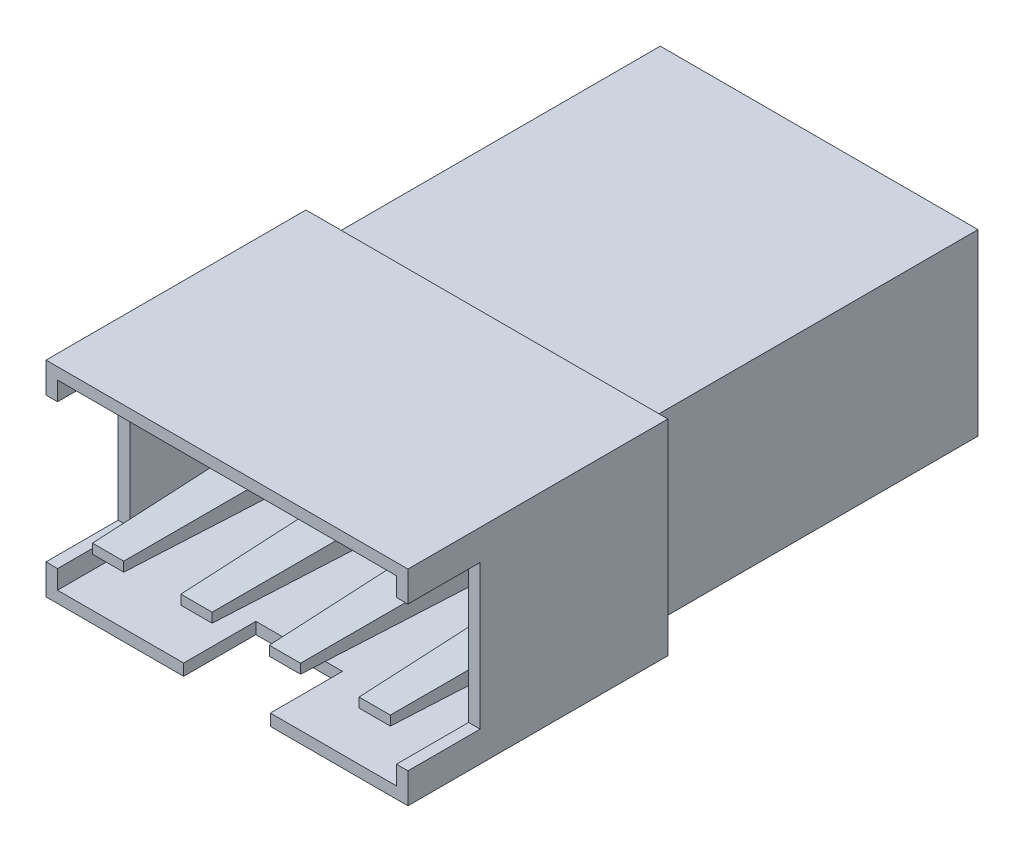
SolidWorks part; units mm, degrees
ref_plane "Front Plane" through (0, 0, 0) normal (0, 0, 1) x (1, 0, 0)
ref_plane "Top Plane" through (0, 0, 0) normal (0, 1, 0) x (1, 0, 0)
ref_plane "Right Plane" through (0, 0, 0) normal (1, 0, 0) x (0, 0, -1)
sketch "Sketch1" plane through (0, 0, 0) normal (0, 0, 1) x (1, 0, 0)
  line L1 (0, 0) -> (12.53, 0)
  line L2 (0, 0) -> (0, -7.1)
  line L3 (0, -7.1) -> (12.53, -7.1)
  line L4 (12.53, 0) -> (12.53, -7.1)
  dimension "D1" = 7.1
  dimension "D2" = 12.53
extrude "Boss-Extrude1" add sketch "Sketch1" against normal blind 9
sketch "Sketch2" plane through (0, 0, 0) normal (0, 0, 1) x (1, 0, 0)
  line L0 (0, 0) -> (0, -7.1) construction
  line L1 (0.4, -0.4) -> (12.13, -0.4)
  line L2 (0.4, -0.4) -> (0.4, -6.7)
  line L3 (0.4, -6.7) -> (12.13, -6.7)
  line L4 (12.13, -0.4) -> (12.13, -6.7)
  line L5 (12.53, -7.1) -> (12.53, 0) construction
  line L6 (12.53, 0) -> (0, 0) construction
  line L7 (0, -7.1) -> (12.53, -7.1) construction
  dimension "D1" = 0.4
  dimension "D2" = 0.4
  dimension "D3" = 0.4
  dimension "D4" = 0.4
extrude "Cut-Extrude1" cut sketch "Sketch2" against normal blind 8.5
sketch "Sketch4" plane through (0, 0, 0) normal (0, 0, 1) x (1, 0, 0)
  line L0 (0, 0) -> (0, -7.1) construction
  line L1 (0, -1.05) -> (0.4, -1.05)
  line L2 (0, -1.05) -> (0, -6.05)
  line L3 (0, -6.05) -> (0.4, -6.05)
  line L4 (0.4, -1.05) -> (0.4, -6.05)
  line L5 (0.4, -0.4) -> (0.4, -6.7) construction
  line L6 (0, -7.1) -> (12.53, -7.1) construction
  line L8 (12.127, -1.05) -> (12.53, -1.05)
  line L9 (12.127, -1.05) -> (12.127, -6.05)
  line L10 (12.127, -6.05) -> (12.53, -6.05)
  line L11 (12.53, -1.05) -> (12.53, -6.05)
  line L12 (0.4, -6.7) -> (12.13, -6.7) construction
  line L13 (4.765, -6.7) -> (7.765, -6.7)
  line L14 (4.765, -6.7) -> (4.765, -7.1)
  line L15 (4.765, -7.1) -> (7.765, -7.1)
  line L16 (7.765, -6.7) -> (7.765, -7.1)
  line L17 (12.53, -7.1) -> (12.53, 0) construction
  dimension "D1" = 5
  dimension "D2" = 1.05
  dimension "D3" = 5
  dimension "D4" = 1.05
  dimension "D5" = 3
  dimension "D6" = 4.765
extrude "Cut-Extrude3" cut sketch "Sketch4" against normal blind 2.5
sketch "Sketch5" plane through (0, 0, -8.5) normal (0, 0, 1) x (1, 0, 0)
  line L0 (0.4, -6.05) -> (0.4, -1.05) construction
  line L1 (0.9, -4.9737) -> (2.4, -4.9737)
  line L2 (0.9, -4.9737) -> (0.9, -5.7239)
  line L3 (0.9, -5.7239) -> (2.4, -5.7239)
  line L4 (2.4, -4.9737) -> (2.4, -5.7239)
  line L5 (0.9, -4.9737) -> (2.4, -5.7239) construction
  line L6 (0.9, -5.7239) -> (2.4, -4.9737) construction
  line L11 (3.96, -4.9737) -> (5.46, -4.9737)
  line L12 (3.96, -4.9737) -> (3.96, -5.7239)
  line L13 (3.96, -5.7239) -> (5.46, -5.7239)
  line L14 (5.46, -4.9737) -> (5.46, -5.7239)
  line L15 (7.02, -4.9737) -> (8.52, -4.9737)
  line L16 (7.02, -4.9737) -> (7.02, -5.7239)
  line L17 (7.02, -5.7239) -> (8.52, -5.7239)
  line L18 (8.52, -4.9737) -> (8.52, -5.7239)
  line L19 (10.13, -4.9737) -> (11.63, -4.9737)
  line L20 (10.13, -4.9737) -> (10.13, -5.7239)
  line L21 (10.13, -5.7239) -> (11.63, -5.7239)
  line L22 (11.63, -4.9737) -> (11.63, -5.7239)
  line L23 (12.13, -1.05) -> (12.13, -6.05) construction
  line L24 (0.4, -6.7) -> (12.13, -6.7) construction
  point P0 (1.65, -5.3488)
  dimension "D1" = 1.5
  dimension "D2" = 1.5
  dimension "D3" = 1.5
  dimension "D4" = 1.5
  dimension "D5" = 0.7502
  dimension "D6" = 0.7502
  dimension "D7" = 0.7502
  dimension "D8" = 0.7502
  dimension "D9" = 0.5
  dimension "D10" = 0.5
  dimension "D11" = 1.56
  dimension "D12" = 1.56
  dimension "D13" = 0.9761
extrude "Boss-Extrude4" add sketch "Sketch5" along normal blind 8 draft 1.5
sketch "Sketch8" plane through (0, 0, -9) normal (0, 0, -1) x (-1, 0, 0)
  line L0 (-12.53, -7.1) -> (-12.53, 0) construction
  line L1 (-11.765, -0.4558) -> (-0.765, -0.4558)
  line L2 (-11.765, -0.4558) -> (-11.765, -6.6484)
  line L3 (-11.765, -6.6484) -> (-0.765, -6.6484)
  line L4 (-0.765, -0.4558) -> (-0.765, -6.6484)
  dimension "D1" = 11
  dimension "D2" = 0.765
extrude "Boss-Extrude5" add sketch "Sketch8" along normal blind 11.5
